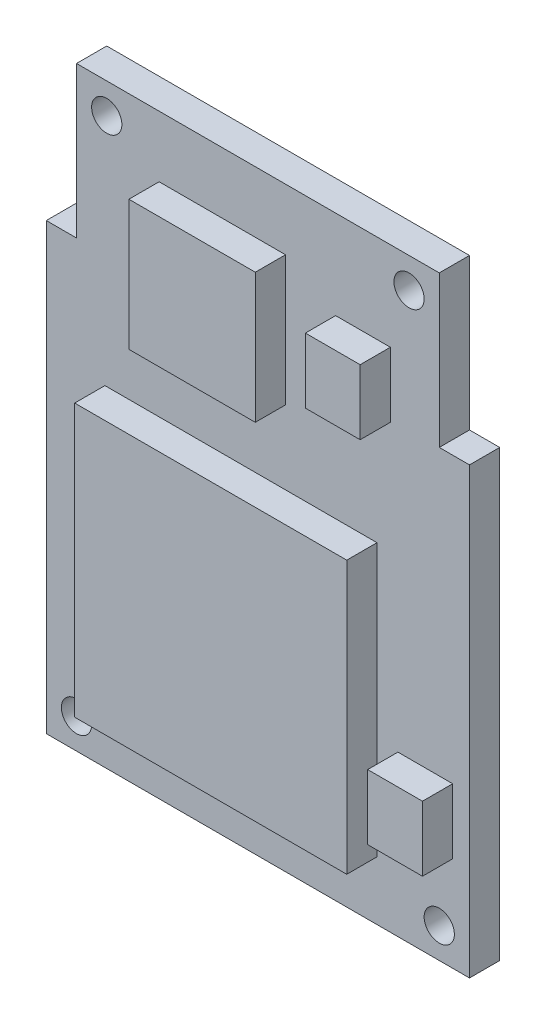
SolidWorks part; units mm, degrees
ref_plane "Front" through (0, 0, 0) normal (0, 0, 1) x (1, 0, 0)
ref_plane "Top" through (0, 0, 0) normal (0, 1, 0) x (1, 0, 0)
ref_plane "Right" through (0, 0, 0) normal (1, 0, 0) x (0, 0, -1)
sketch "草图1" plane through (0, 0, 0) normal (0, 0, 1) x (1, 0, 0)
  line L1 (7, -7.35) -> (-7, -7.35)
  line L2 (7, -7.35) -> (7, 7.35)
  line L3 (7, 7.35) -> (-7, 7.35)
  line L4 (-7, -7.35) -> (-7, 7.35)
  line L5 (7, -7.35) -> (-7, 7.35) construction
  line L6 (7, 7.35) -> (-7, -7.35) construction
  point P0 (0, 0)
  dimension "D1" = 14
  dimension "D2" = 14.7
extrude "凸台-拉伸1" add sketch "草图1" along normal blind 1
sketch "草图2" plane through (0, 0, 0) normal (0, 0, 1) x (1, 0, 0)
  line L5 (0, 14.719) -> (0, -10.2493) construction
  line L6 (7, 7.35) -> (-7, 7.35) construction
  line L7 (6, 7.35) -> (-6, 7.35)
  line L8 (6, 7.35) -> (6, 12.35)
  line L9 (6, 12.35) -> (-6, 12.35)
  line L10 (-6, 7.35) -> (-6, 12.35)
  line L11 (6, 7.35) -> (-6, 12.35) construction
  line L12 (6, 12.35) -> (-6, 7.35) construction
  point P2 (0, 9.85)
  dimension "D1" = 12
  dimension "D2" = 5
extrude "凸台-拉伸2" add sketch "草图2" along normal blind 1
sketch "草图3" plane through (0, 0, 1) normal (0, 0, 1) x (1, 0, 0)
  line L0 (0, 16.2659) -> (0, -11.3855) construction
  line L3 (-7, 7.35) -> (-7, -7.35) construction
  circle A0 centre (-5, 11.35) radius 0.5
  circle A1 centre (5, 11.35) radius 0.5
  circle A2 centre (-6, -6.35) radius 0.5
  circle A4 centre (6, -6.35) radius 0.5
  dimension "D1" = 1
  dimension "D2" = 10
  dimension "D3" = 12
  dimension "D6" = 1
  dimension "D7" = 17.7
extrude "切除-拉伸1" cut sketch "草图3" against normal through all
sketch "草图4" plane through (0, 0, 1) normal (0, 0, 1) x (1, 0, 0)
  line L0 (0.9141, 6.0262) -> (-3.2672, 6.0262)
  line L1 (3.9399, -5.4089) -> (-5.0601, -5.4089)
  line L2 (3.9399, -5.4089) -> (3.9399, 3.5911)
  line L3 (3.9399, 3.5911) -> (-5.0601, 3.5911)
  line L4 (-5.0601, -5.4089) -> (-5.0601, 3.5911)
  line L5 (3.9399, -5.4089) -> (-5.0601, 3.5911) construction
  line L6 (3.9399, 3.5911) -> (-5.0601, -5.4089) construction
  line L7 (0.9141, 6.0262) -> (0.9141, 10.3269)
  line L8 (0.9141, 10.3269) -> (-3.2672, 10.3269)
  line L9 (-3.2672, 6.0262) -> (-3.2672, 10.3269)
  line L10 (4.3828, 7.2613) -> (2.5711, 7.2613)
  line L11 (4.3828, 7.2613) -> (4.3828, 9.4117)
  line L12 (4.3828, 9.4117) -> (2.5711, 9.4117)
  line L13 (2.5711, 7.2613) -> (2.5711, 9.4117)
  line L14 (6.4441, -4.2131) -> (4.6324, -4.2131)
  line L15 (6.4441, -4.2131) -> (6.4441, -2.0627)
  line L16 (6.4441, -2.0627) -> (4.6324, -2.0627)
  line L17 (4.6324, -4.2131) -> (4.6324, -2.0627)
  point P0 (-0.5601, -0.9089)
  dimension "D1" = 9
  dimension "D2" = 9
extrude "凸台-拉伸3" add sketch "草图4" along normal blind 1
sketch "草图5" plane through (0, 0, 0) normal (0, 0, -1) x (-1, 0, 0)
  line L0 (6, -4.35) -> (4.0109, -4.35)
  line L1 (-1.7133, 5.4285) -> (-4.1836, 5.4285)
  line L2 (-1.7133, 5.4285) -> (-1.7133, 7.8191)
  line L3 (-1.7133, 7.8191) -> (-4.1836, 7.8191)
  line L4 (-4.1836, 5.4285) -> (-4.1836, 7.8191)
  line L5 (-1.7133, 5.4285) -> (-4.1836, 7.8191) construction
  line L6 (-1.7133, 7.8191) -> (-4.1836, 5.4285) construction
  line L7 (6, -4.35) -> (6, 3.15)
  line L8 (6, 3.15) -> (4.0109, 3.15)
  line L9 (4.0109, -4.35) -> (4.0109, 3.15)
  line L10 (7, -7.35) -> (-7, -7.35) construction
  line L11 (7, 7.35) -> (7, -7.35) construction
  point P0 (-2.9484, 6.6238)
  dimension "D1" = 7.5
  dimension "D2" = 3
  dimension "D3" = 1
extrude "凸台-拉伸4" add sketch "草图5" along normal blind 1
